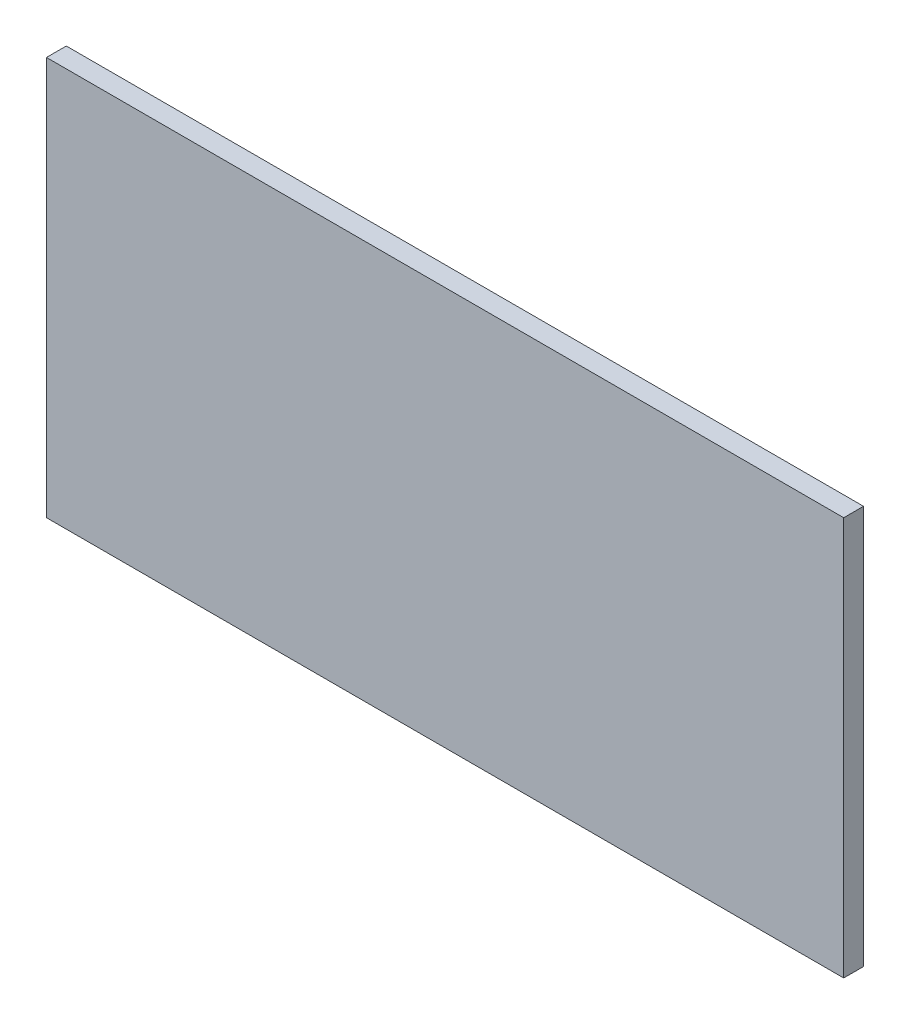
SolidWorks part; units mm, degrees
material "Black Acrylic"
ref_plane "Front Plane" through (0, 0, 0) normal (0, 0, 1) x (1, 0, 0)
ref_plane "Top Plane" through (0, 0, 0) normal (0, 1, 0) x (1, 0, 0)
ref_plane "Right Plane" through (0, 0, 0) normal (1, 0, 0) x (0, 0, -1)
sketch "Sketch1" plane through (0, 0, 0) normal (0, 0, 1) x (1, 0, 0)
  line L1 (-90.5, 90.5) -> (90.5, 90.5)
  line L2 (-90.5, 90.5) -> (-90.5, 0)
  line L3 (-90.5, 0) -> (90.5, 0)
  line L4 (90.5, -90.5) -> (-90.5, 90.5) construction
  line L5 (-90.5, -90.5) -> (90.5, 90.5) construction
  line L6 (90.5, -90.5) -> (90.5, 90.5) construction
  line L7 (90.5, 90.5) -> (90.5, 0)
  point P4 (0, 0)
  dimension "D1" = 181
  dimension "D2" = 181
extrude "Boss-Extrude1" add sketch "Sketch1" along normal mid plane 4.5
